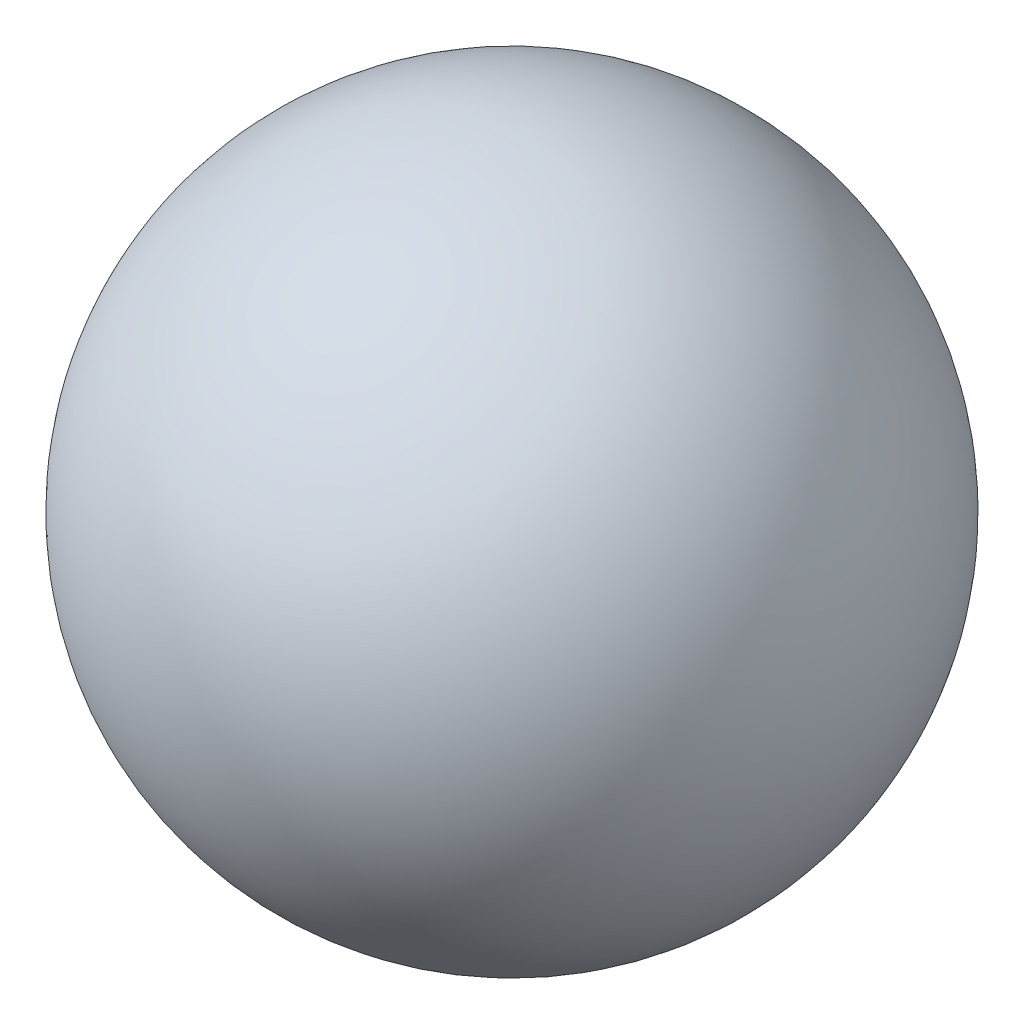
SolidWorks part; units mm, degrees
ref_plane "Płaszczyzna przednia" through (0, 0, 0) normal (0, 0, 1) x (1, 0, 0)
ref_plane "Płaszczyzna górna" through (0, 0, 0) normal (0, 1, 0) x (1, 0, 0)
ref_plane "Płaszczyzna prawa" through (0, 0, 0) normal (1, 0, 0) x (0, 0, -1)
sketch "Sketch1" plane through (0, 0, 0) normal (0, 0, 1) x (1, 0, 0)
  line L0 (-12, 0) -> (12, 0)
  arc A0 (-12, 0) -> (12, 0) centre (0, 0) ccw
  dimension "D1" = 24
revolve "Revolve1" add sketch "Sketch1" angle 360 about L0
